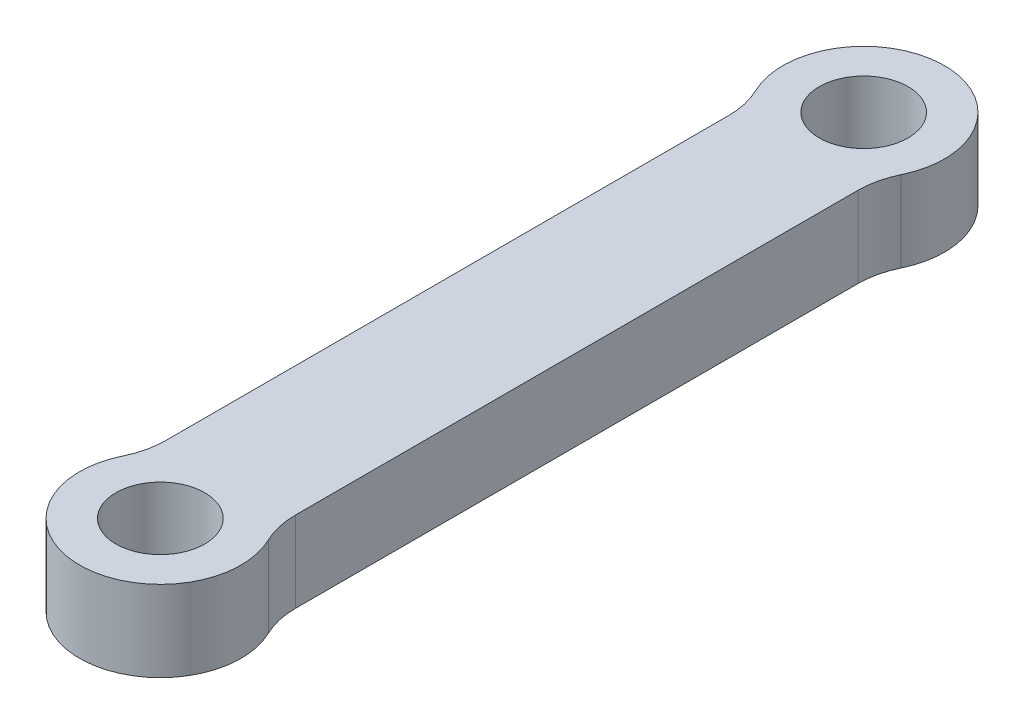
SolidWorks part; units mm, degrees
material "Nylon 101"
ref_plane "Front Plane" through (0, 0, 0) normal (0, 0, 1) x (1, 0, 0)
ref_plane "Top Plane" through (0, 0, 0) normal (0, 1, 0) x (1, 0, 0)
ref_plane "Right Plane" through (0, 0, 0) normal (1, 0, 0) x (0, 0, -1)
sketch "Sketch1" plane through (0, 0, 0) normal (0, 1, 0) x (1, 0, 0)
  line L2 (-4, -21.75) -> (-4, 21.75)
  line L4 (4, -21.75) -> (4, 21.75)
  line L5 (-4, -21.75) -> (4, 21.75) construction
  line L6 (-4, 21.75) -> (4, -21.75) construction
  arc A0 (4, 21.75) -> (-4, 21.75) centre (0, 21.75) ccw
  arc A1 (-4, -21.75) -> (4, -21.75) centre (0, -21.75) ccw
  point P0 (0, 0)
  dimension "D2" = 4
  dimension "D1" = 43.5
extrude "Boss-Extrude1" add sketch "Sketch1" along normal blind 5
ref_plane "Plane1" through (0, 5, 0) normal (0, 1, 0) x (1, 0, 0)
sketch "Sketch2" plane through (0, 5, 0) normal (0, 1, 0) x (1, 0, 0)
  circle A4 centre (0, 21.75) radius 2.75
  circle A5 centre (0, -21.75) radius 2.75
  dimension "D1" = 5.5
extrude "Cut-Extrude2" cut sketch "Sketch2" against normal through all
sketch "Sketch3" plane through (0, 5, 0) normal (0, 1, 0) x (1, 0, 0)
  line L0 (0, 0) -> (5.7918, 0) construction
  circle A0 centre (0, 21.75) radius 5
  circle A1 centre (0, 21.75) radius 2.75
  circle A2 centre (0, 21.75) radius 2.75 construction
  circle A3 centre (0, -21.75) radius 2.75
  circle A4 centre (0, -21.75) radius 5
  dimension "D1" = 10
extrude "Boss-Extrude2" add sketch "Sketch3" against normal up to surface (5 mm away) up to face at (0, 0, -19)
fillet "Fillet1" radius 5 4 edges at (-4, 2.5, 18.75) (4, 2.5, 18.75) (4, 2.5, -18.75) (-4, 2.5, -18.75)
